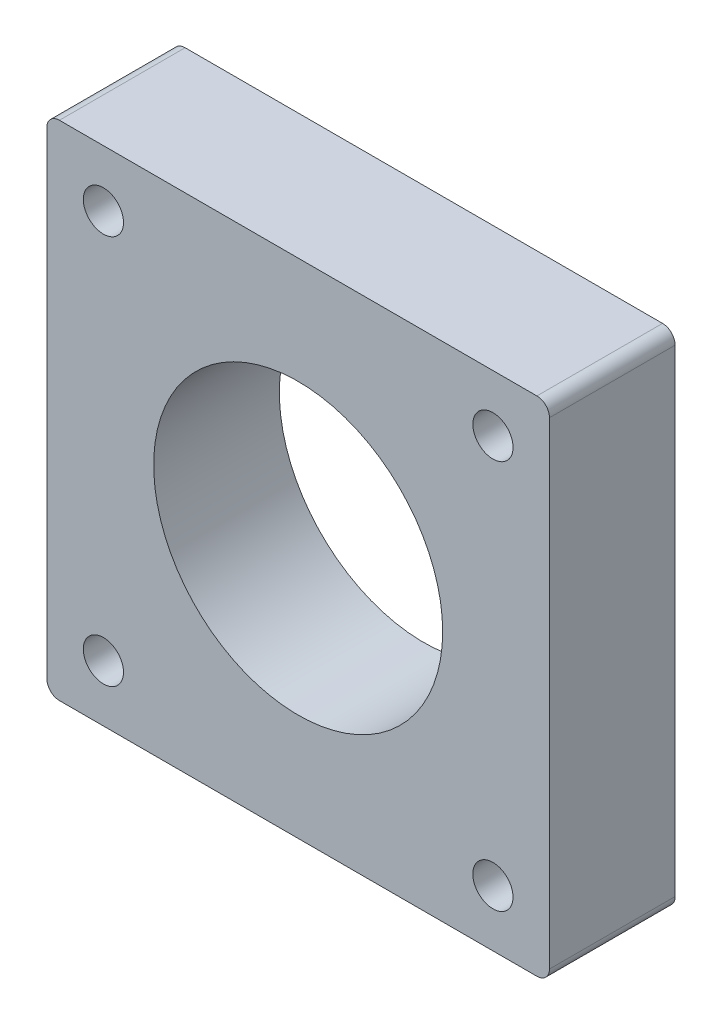
SolidWorks part; units mm, degrees
ref_plane "Front Plane" through (0, 0, 0) normal (0, 0, 1) x (1, 0, 0)
ref_plane "Top Plane" through (0, 0, 0) normal (0, 1, 0) x (1, 0, 0)
ref_plane "Right Plane" through (0, 0, 0) normal (1, 0, 0) x (0, 0, -1)
sketch "Sketch1" plane through (0, 0, 0) normal (0, 0, 1) x (1, 0, 0)
  line L0 (-20, 19) -> (-20, -19)
  line L1 (-15.5, -15.5) -> (15.5, -15.5) construction
  line L2 (-15.5, -15.5) -> (-15.5, 15.5) construction
  line L3 (-15.5, 15.5) -> (15.5, 15.5) construction
  line L4 (15.5, -15.5) -> (15.5, 15.5) construction
  line L5 (-15.5, -15.5) -> (15.5, 15.5) construction
  line L6 (-15.5, 15.5) -> (15.5, -15.5) construction
  line L7 (-19, -20) -> (19, -20)
  line L8 (20, 19) -> (20, -19)
  line L9 (-19, 20) -> (19, 20)
  line L11 (-20, -20) -> (20, 20) construction
  line L12 (-20, 20) -> (20, -20) construction
  circle A0 centre (0, 0) radius 11.5
  circle A1 centre (-15.5, 15.5) radius 1.6
  circle A2 centre (15.5, 15.5) radius 1.6
  circle A3 centre (15.5, -15.5) radius 1.6
  circle A4 centre (-15.5, -15.5) radius 1.6
  arc A5 (-20, -19) -> (-19, -20) centre (-19, -19) ccw
  arc A6 (19, -20) -> (20, -19) centre (19, -19) ccw
  arc A7 (20, 19) -> (19, 20) centre (19, 19) ccw
  arc A8 (-20, 19) -> (-19, 20) centre (-19, 19) cw
  point P0 (0, 0)
  point P36 (-20, 6)
  point P43 (20, 6)
  point P44 (0, 20)
  dimension "D3" = 23
  dimension "D4" = 40
  dimension "D6" = 1
  dimension "D1" = 31
  dimension "D2" = 31
  dimension "D5" = 40
extrude "Boss-Extrude1" add sketch "Sketch1" along normal blind 10
